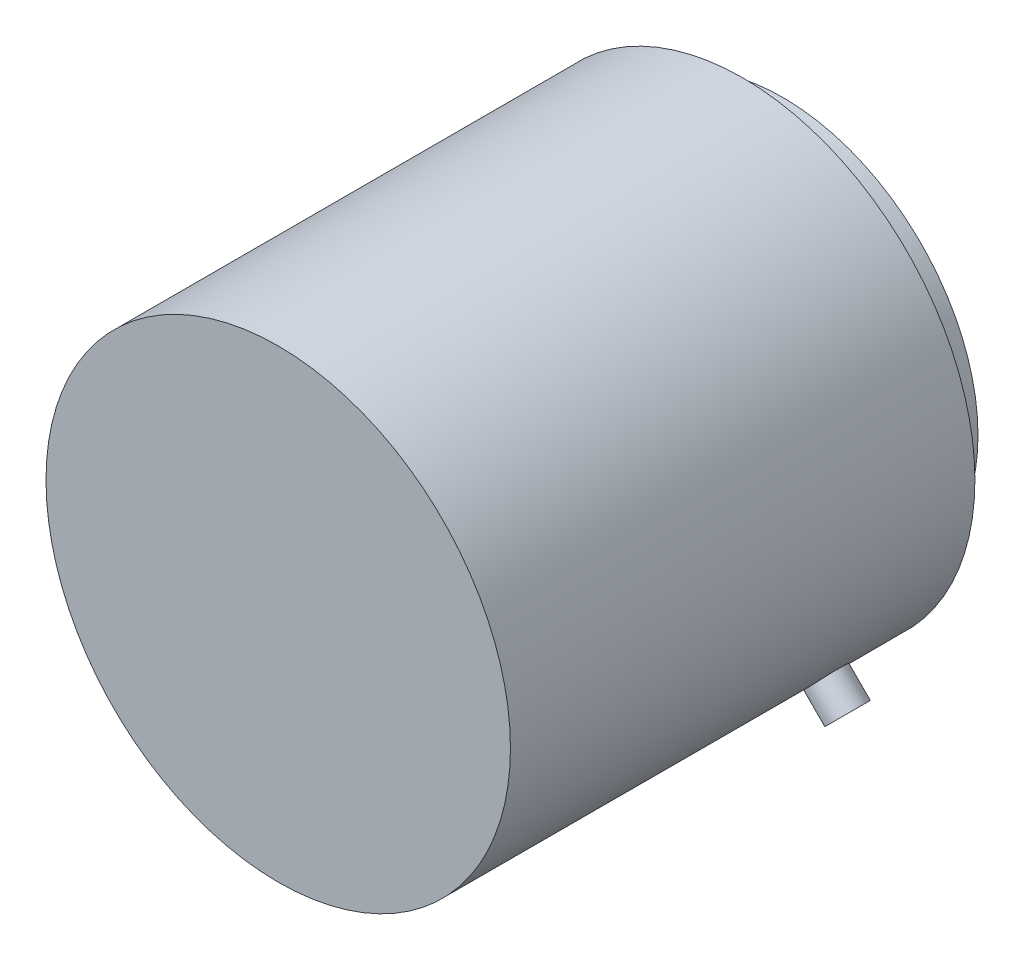
SolidWorks part; units mm, degrees
ref_plane "Front Plane" through (0, 0, 0) normal (0, 0, 1) x (1, 0, 0)
ref_plane "Top Plane" through (0, 0, 0) normal (0, 1, 0) x (1, 0, 0)
ref_plane "Right Plane" through (0, 0, 0) normal (1, 0, 0) x (0, 0, -1)
sketch "Sketch1" plane through (0, 0, 0) normal (0, 0, 1) x (1, 0, 0)
  circle A0 centre (0, 0) radius 37.5
  dimension "D1" = 75
extrude "Boss-Extrude1" add sketch "Sketch1" along normal blind 75
sketch "Sketch2" plane through (0, 0, 0) normal (0, 0, -1) x (-1, 0, 0)
  circle A0 centre (0, 0) radius 31.5
  dimension "D1" = 63
extrude "Boss-Extrude2" add sketch "Sketch2" along normal blind 6.5
sketch "Sketch3" plane through (0, 0, -6.5) normal (0, 0, -1) x (-1, 0, 0)
  circle A0 centre (0, 0) radius 15.75
  dimension "D1" = 31.5
extrude "Cut-Extrude1" cut sketch "Sketch3" against normal blind 6.5
sketch "Sketch4" plane through (0, 0, -6.5) normal (0, 0, -1) x (-1, 0, 0)
  circle A0 centre (25, 0) radius 3
  circle A1 centre (0, -25) radius 3
  circle A2 centre (-25, 0) radius 3
  circle A3 centre (0, 25) radius 3
  circle A4 centre (0, 0) radius 25
  dimension "D1" = 50
extrude "Cut-Extrude2" cut sketch "Sketch4" against normal blind 5 contours A0 A4 | A4 A3 | A3 A4 | A2 | A1
sketch "Sketch6" plane through (0, 0, 0) normal (0, 0, -1) x (-1, 0, 0)
  line L0 (0, 0) -> (-41.0527, -41.0527)
  line L1 (-22.1632, -26.4059) -> (-26.4059, -22.1632)
  line L2 (-22.1632, -26.4059) -> (-27.8201, -32.0627)
  line L3 (-27.8201, -32.0627) -> (-32.0627, -27.8201)
  line L4 (-32.0627, -27.8201) -> (-26.4059, -22.1632)
  circle M7 centre (0, 0) radius 37.5
  dimension "D1" = 6
  dimension "D2" = 3
  dimension "D3" = 8
extrude "Boss-Extrude3" add sketch "Sketch6" against normal blind 6 from offset 10 contours L3 L2 L0 M7 | L4 L3 L0 M7 offset against normal yes
sketch "Sketch7" plane through (29.9414, -29.9414, 0) normal (0.7071, -0.7071, 0) x (0, 0, -1)
  circle A0 centre (-13, 0) radius 3
  circle A1 centre (-13, 0) radius 7.956
extrude "Cut-Extrude4" cut sketch "Sketch7" against normal up to surface (4.9637 mm away)
